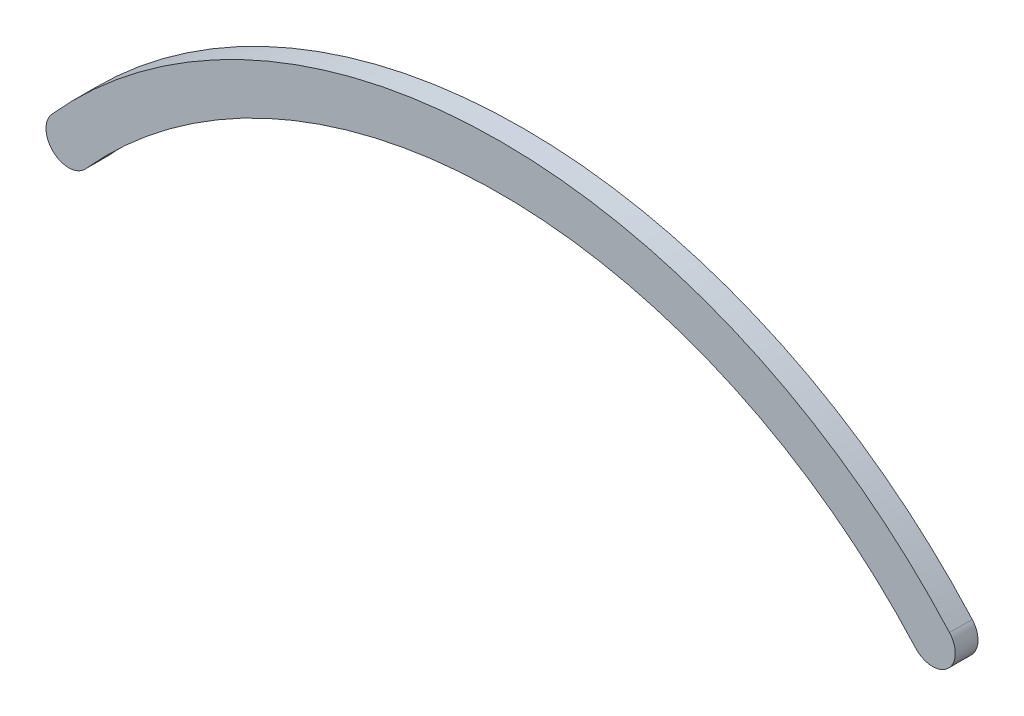
SolidWorks part; units mm, degrees
ref_plane "Alzado" through (0, 0, 0) normal (0, 0, 1) x (1, 0, 0)
ref_plane "Planta" through (0, 0, 0) normal (0, 1, 0) x (1, 0, 0)
ref_plane "Vista lateral" through (0, 0, 0) normal (1, 0, 0) x (0, 0, -1)
sketch "Croquis1" plane through (0, 0, 0) normal (0, 0, 1) x (1, 0, 0)
  line L0 (-120.65, 0) -> (120.65, 0) construction
  arc A0 (-125.385, 4.2311) -> (-115.9134, -4.2294) centre (-120.65, 0) ccw
  arc A1 (115.9134, -4.2294) -> (125.385, 4.2311) centre (120.65, 0) ccw
  arc A2 (-125.385, 4.2311) -> (125.385, 4.2311) centre (0, -107.8089) cw
  arc A3 (-115.9134, -4.2294) -> (115.9134, -4.2294) centre (0, -107.7306) cw
  point P4 (0, 0)
  dimension "D2" = 12.7
  dimension "D3" = 12.7
  dimension "D4" = 155.3977
  dimension "D5" = 168.1498
  dimension "D1" = 241.3
extrude "Saliente-Extruir1" add sketch "Croquis1" along normal blind 6.35
